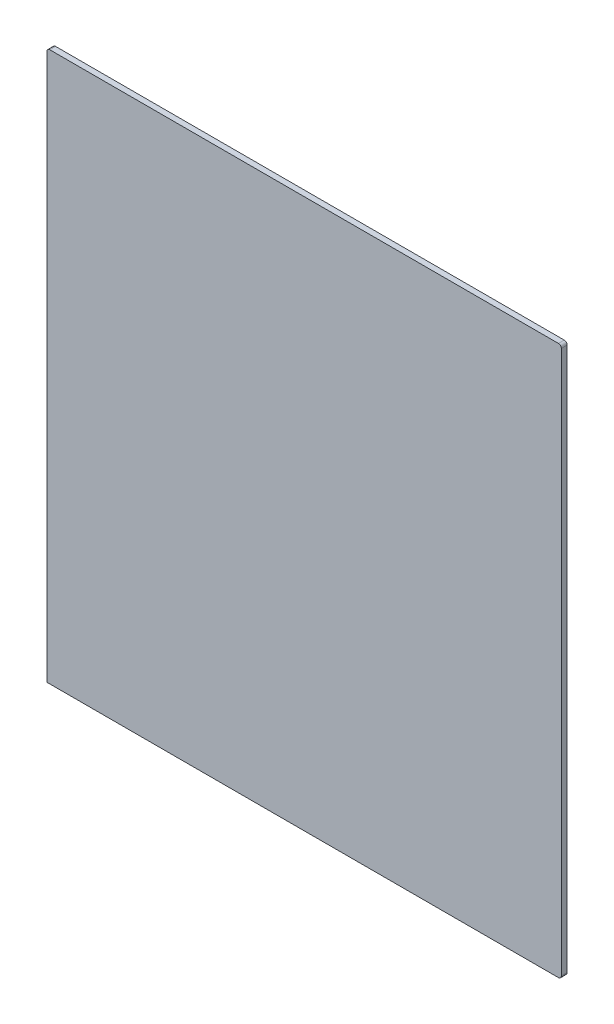
SolidWorks part; units mm, degrees
ref_plane "前视基准面" through (0, 0, 0) normal (0, 0, 1) x (1, 0, 0)
ref_plane "上视基准面" through (0, 0, 0) normal (0, 1, 0) x (1, 0, 0)
ref_plane "右视基准面" through (0, 0, 0) normal (1, 0, 0) x (0, 0, -1)
sketch "草图1" plane through (0, 0, 0) normal (0, 0, 1) x (1, 0, 0)
  line L0 (-65.6111, 40.2757) -> (198.8889, 40.2757)
  line L1 (200.3889, 41.7757) -> (200.3889, 322.7757)
  line L2 (198.8889, 324.2757) -> (-64.1111, 324.2757)
  line L3 (-65.6111, 322.7757) -> (-65.6111, 40.2757)
  arc A0 (198.8889, 324.2757) -> (200.3889, 322.7757) centre (198.8889, 322.7757) cw
  arc A1 (200.3889, 41.7757) -> (198.8889, 40.2757) centre (198.8889, 41.7757) cw
  arc A2 (-64.1111, 324.2757) -> (-65.6111, 322.7757) centre (-64.1111, 322.7757) ccw
  dimension "D1" = 1.5
extrude "凸台-拉伸1" add sketch "草图1" along normal blind 3
